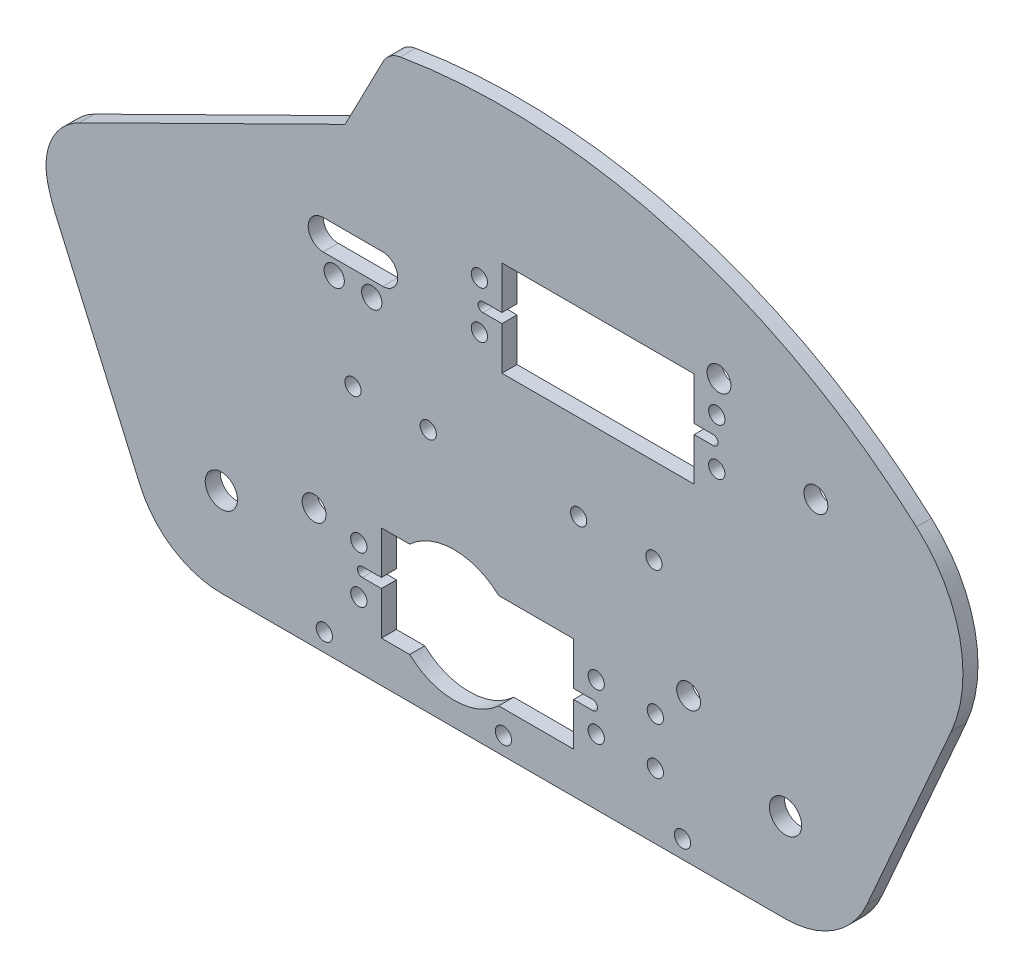
SolidWorks part; units mm, degrees
ref_plane "Front Plane" through (0, 0, 0) normal (0, 0, 1) x (1, 0, 0)
ref_plane "Top Plane" through (0, 0, 0) normal (0, 1, 0) x (1, 0, 0)
ref_plane "Right Plane" through (0, 0, 0) normal (1, 0, 0) x (0, 0, -1)
sketch "Sketch1" plane through (0, 0, 0) normal (0, 0, 1) x (1, 0, 0)
  line L8 (0, 18.9078) -> (120.015, 18.9078) construction
  line L18 (155.2575, 52.1157) -> (-35.2425, 52.1157) construction
  line L37 (0, 0) -> (120.015, 0)
  line L42 (19.7347, 25.5664) -> (0, 18.9078) construction
  line L54 (155.2575, 52.1157) -> (137.3256, 11.3022)
  line L55 (60.0075, 52.1157) -> (60.0075, 18.9078) construction
  line L56 (-35.2425, 52.1157) -> (-17.3106, 11.3022)
  line L58 (147.8628, 86.1549) -> (-27.8478, 86.1549) construction
  circle A21 centre (120.015, 18.9078) radius 3.429
  circle A22 centre (0, 18.9078) radius 3.429
  arc A25 (137.3256, 11.3022) -> (120.015, 0) centre (120.015, 18.9078) cw
  arc A26 (0, 0) -> (-17.3106, 11.3022) centre (0, 18.9078) cw
  circle A27 centre (19.7347, 25.5664) radius 2.54
  arc A28 (147.8628, 86.1549) -> (-27.8478, 86.1549) centre (60.0075, -12.2157) ccw
  arc A29 (147.8628, 86.1549) -> (155.2575, 52.1157) centre (128.1135, 64.0417) cw
  arc A30 (-27.8478, 86.1549) -> (-35.2425, 52.1157) centre (-8.0985, 64.0417) ccw
  dimension "D5" = 18.9078
  dimension "D8" = 29.6484
  dimension "D3" = 52.1157
  dimension "D2" = 6.858
  dimension "D10" = 5.08
  dimension "D1" = 190.5
  dimension "D4" = 18.645
  dimension "D6" = 20.8278
  dimension "D7" = 120.015
  dimension "D9" = 34.0392
extrude "Boss-Extrude1" add sketch "Sketch1" along normal blind 3.2004
sketch "Sketch2" plane through (0, 0, 0) normal (0, 0, -1) x (-1, 0, 0)
  line L1 (-155.2575, 52.1157) -> (35.2425, 52.1157) construction
  line L28 (-92.0115, 52.1157) -> (-76.0095, 52.1157) construction
  line L29 (-76.0095, 52.1157) -> (-44.0055, 52.1157) construction
  line L30 (-44.0055, 52.1157) -> (-28.0035, 52.1157) construction
  circle A0 centre (-92.0115, 52.1157) radius 1.7272
  circle A1 centre (-76.0095, 52.1157) radius 1.7272
  circle A2 centre (-44.0055, 52.1157) radius 1.7272
  circle A3 centre (-28.0035, 52.1157) radius 1.7272
  point P11 (-36.0045, 52.1157)
  point P16 (-84.0105, 52.1157)
  dimension "D3" = 3.4544
  dimension "D2" = 16.002
  dimension "D4" = 48.006
extrude "Cut-Extrude1" cut sketch "Sketch2" against normal blind 3.2004
sketch "Sketch5" plane through (0, 0, 0) normal (0, 0, -1) x (-1, 0, 0)
  line L0 (0, 18.9078) -> (-120.015, 18.9078) construction
  line L5 (-92.3222, 13.9078) -> (-92.3222, 23.9078) construction
  line L6 (-74.944, 29.0678) -> (-74.944, 8.7478)
  line L7 (-34.05, 29.0678) -> (-34.05, 8.7478)
  line L12 (-54.497, 29.0678) -> (-54.497, 8.7478) construction
  line L13 (-79.747, 13.9078) -> (-79.747, 23.9078) construction
  line L14 (-29.247, 13.9078) -> (-29.247, 23.9078) construction
  line L15 (-79.747, 18.9078) -> (-29.247, 18.9078) construction
  line L19 (-92.3222, 18.9078) -> (-79.747, 18.9078) construction
  line L21 (-74.944, 8.7478) -> (-34.05, 8.7478)
  line L25 (-74.944, 29.0678) -> (-34.05, 29.0678)
  circle A0 centre (-79.747, 23.9078) radius 1.7272
  circle A1 centre (-29.247, 13.9078) radius 1.7272
  circle A2 centre (-29.247, 23.9078) radius 1.7272
  circle A3 centre (-79.747, 13.9078) radius 1.7272
  circle A6 centre (0, 18.9078) radius 3.429 construction
  circle A9 centre (-92.3222, 23.9078) radius 1.7272
  circle A10 centre (-92.3222, 13.9078) radius 1.7272
  point P8 (-44.45, 18.9078)
  point P9 (-54.497, 18.9078)
  dimension "D2" = 3.4544
  dimension "D3" = 40.894
  dimension "D5" = 10.4
  dimension "D1" = 50.5
  dimension "D4" = 20.32
  dimension "D6" = 44.45
  dimension "D7" = 10
  dimension "D8" = 12.5752
extrude "Cut-Extrude3" cut sketch "Sketch5" against normal through all
sketch "Sketch6" plane through (0, 0, 3.2004) normal (0, 0, 1) x (1, 0, 0)
  line L3 (79.747, 18.9078) -> (29.247, 18.9078) construction
  line L4 (29.986, 19.9238) -> (34.05, 19.9238)
  line L5 (29.986, 19.9238) -> (29.986, 17.8918) construction
  line L7 (29.986, 17.8918) -> (34.05, 17.8918)
  line L8 (34.05, 19.9238) -> (34.05, 17.8918)
  line L9 (74.944, 19.9238) -> (79.008, 19.9238)
  line L10 (74.944, 19.9238) -> (74.944, 17.8918)
  line L11 (74.944, 17.8918) -> (79.008, 17.8918)
  line L12 (79.008, 19.9238) -> (79.008, 17.8918) construction
  line L13 (34.05, 8.7478) -> (34.05, 29.0678) construction
  line L14 (74.944, 29.0678) -> (74.944, 8.7478) construction
  arc A6 (79.008, 19.9238) -> (79.008, 17.8918) centre (79.008, 18.9078) cw
  arc A7 (29.986, 19.9238) -> (29.986, 17.8918) centre (29.986, 18.9078) ccw
  point P22 (34.05, 18.9078)
  point P23 (74.944, 18.9078)
  dimension "D4" = 4.064
  dimension "D5" = 2.032
extrude "Cut-Extrude4" cut sketch "Sketch6" against normal up to surface (3.2004 mm away) up to face at (90.595, 23.9078, 0)
sketch "Sketch8" plane through (0, 0, 3.2004) normal (0, 0, 1) x (1, 0, 0)
  line L0 (21.9075, 3.81) -> (98.1075, 3.81) construction
  line L1 (60.0075, 7.62) -> (60.0075, 0) construction
  line L2 (0, 0) -> (120.015, 0) construction
  circle A0 centre (21.9075, 3.81) radius 1.7272
  circle A1 centre (60.0075, 3.81) radius 1.7272
  circle A2 centre (98.1075, 3.81) radius 1.7272
  point P6 (60.0075, 3.81)
  dimension "D3" = 3.4544
  dimension "D1" = 76.2
  dimension "D2" = 7.62
extrude "Cut-Extrude6" cut sketch "Sketch8" against normal up to surface (3.2004 mm away) up to face at (54.497, 18.9078, 0)
sketch "Sketch9" plane through (0, 0, 0) normal (0, 0, -1) x (-1, 0, 0)
  line L5 (-29.247, 13.9078) -> (-29.247, 23.9078) construction
  line L7 (-80.1415, 90.6958) -> (-80.1415, 70.3758) construction
  line L12 (-59.6945, 90.6958) -> (-59.6945, 70.3758)
  line L13 (-54.497, 29.0678) -> (-54.497, 8.7478) construction
  line L14 (-74.944, 8.7478) -> (-34.05, 8.7478) construction
  line L18 (-100.5885, 70.3758) -> (-100.5885, 90.6958)
  line L19 (-105.3915, 75.5358) -> (-105.3915, 85.5358) construction
  line L20 (-54.8915, 75.5358) -> (-54.8915, 85.5358) construction
  line L24 (-105.3915, 80.5358) -> (-54.8915, 80.5358) construction
  line L30 (-100.5885, 70.3758) -> (-59.6945, 70.3758)
  line L31 (-100.5885, 90.6958) -> (-59.6945, 90.6958)
  line L32 (-105.8603, 92.4374) -> (-126.4745, 80.5358) construction
  line L34 (-126.4745, 80.5358) -> (-111.6995, 46.9073) construction
  line L35 (-111.6995, 46.9073) -> (-146.2916, 31.7089) construction
  line L37 (-137.3256, 11.3022) -> (-155.2575, 52.1157) construction
  line L38 (-34.05, 29.0678) -> (-34.05, 8.7478) construction
  circle A6 centre (-19.7347, 25.5664) radius 2.54 construction
  circle A7 centre (-105.3915, 85.5358) radius 1.7272
  circle A8 centre (-105.8603, 92.4374) radius 2.54
  circle A9 centre (-54.8915, 75.5358) radius 1.7272
  circle A10 centre (-54.8915, 85.5358) radius 1.7272
  circle A11 centre (-105.3915, 75.5358) radius 1.7272
  circle A13 centre (-126.4745, 80.5358) radius 2.54
  point P14 (-80.1415, 80.5358)
  point P21 (-89.9915, 80.5358)
  dimension "D2" = 30
  dimension "D3" = 37.7837
  dimension "D5" = 3.4544
  dimension "D6" = 15.4
  dimension "D4" = 36.7311
  dimension "D7" = 23.8032
  dimension "D8" = 50.5
extrude "Cut-Extrude8" cut sketch "Sketch9" against normal up to surface (3.2004 mm away) up to face at (23.6347, 3.81, 3.2004)
sketch "Sketch10" plane through (0, 0, 3.2004) normal (0, 0, 1) x (1, 0, 0)
  line L0 (-24.9698, 88.6515) -> (-19.2074, 77.0076)
  line L1 (-19.2074, 77.0076) -> (26.3335, 99.5452)
  line L2 (26.3335, 99.5452) -> (35.569, 117.3917)
  arc A2 (35.569, 117.3917) -> (-24.9698, 88.6515) centre (60.0075, -12.2157) ccw
  arc A4 (147.8628, 86.1549) -> (-27.8478, 86.1549) centre (60.0075, -12.2157) ccw construction
  dimension "D1" = 50.8126
  dimension "D2" = 20.0946
  dimension "D3" = 12.9917
  dimension "D4" = 143.691
  dimension "D5" = 3.81
extrude "Cut-Extrude9" cut sketch "Sketch10" against normal up to surface (3.2004 mm away) up to face at (103.6643, 75.5358, 0)
fillet "Fillet1" radius 5.08 2 edges at (35.569, 117.3917, 1.6002) (-24.9698, 88.6515, 1.6002)
sketch "Sketch11" plane through (0, 0, 0) normal (0, 0, -1) x (-1, 0, 0)
  line L1 (-34.3535, 80.0557) -> (-21.6535, 80.0557)
  line L2 (-34.3535, 80.0557) -> (-34.3535, 73.7057) construction
  line L3 (-34.3535, 73.7057) -> (-21.6535, 73.7057)
  line L4 (-21.6535, 80.0557) -> (-21.6535, 73.7057) construction
  line L7 (0, 0) -> (-120.015, 0) construction
  line L9 (-32.004, 70.5307) -> (-24.003, 70.5307) construction
  line L11 (-28.0035, 73.7057) -> (-28.0035, 70.5307) construction
  arc A0 (-21.6535, 80.0557) -> (-21.6535, 73.7057) centre (-21.6535, 76.8807) cw
  arc A1 (-34.3535, 80.0557) -> (-34.3535, 73.7057) centre (-34.3535, 76.8807) ccw
  circle A5 centre (-28.0035, 52.1157) radius 1.7272 construction
  circle A6 centre (-32.004, 70.5307) radius 2.159
  circle A7 centre (-24.003, 70.5307) radius 2.159
  dimension "D3" = 21.59
  dimension "D7" = 4.318
  dimension "D1" = 12.7
  dimension "D2" = 6.35
  dimension "D4" = 6.35
  dimension "D5" = 3.175
  dimension "D6" = 8.001
extrude "Cut-Extrude10" cut sketch "Sketch11" against normal up to surface (3.2004 mm away) up to face at (41.5205, 61.5939, 3.2004)
sketch "Sketch12" plane through (0, 0, 0) normal (0, 0, -1) x (-1, 0, 0)
  line L0 (-100.5885, 90.6958) -> (-100.5885, 70.3758) construction
  line L1 (-59.6945, 70.3758) -> (-59.6945, 90.6958) construction
  line L4 (-104.6525, 81.5518) -> (-100.5885, 81.5518)
  line L5 (-104.6525, 81.5518) -> (-104.6525, 79.5198) construction
  line L7 (-104.6525, 79.5198) -> (-100.5885, 79.5198)
  line L8 (-100.5885, 81.5518) -> (-100.5885, 79.5198)
  line L9 (-59.6945, 81.5518) -> (-55.6305, 81.5518)
  line L10 (-59.6945, 81.5518) -> (-59.6945, 79.5198)
  line L11 (-59.6945, 79.5198) -> (-55.6305, 79.5198)
  line L12 (-55.6305, 81.5518) -> (-55.6305, 79.5198) construction
  arc A6 (-55.6305, 81.5518) -> (-55.6305, 79.5198) centre (-55.6305, 80.5358) cw
  arc A7 (-104.6525, 81.5518) -> (-104.6525, 79.5198) centre (-104.6525, 80.5358) ccw
  point P22 (-100.5885, 80.5358)
  point P23 (-59.6945, 80.5358)
  dimension "D4" = 4.064
  dimension "D5" = 2.032
extrude "Cut-Extrude11" cut sketch "Sketch12" against normal up to surface (3.2004 mm away) up to face at (28.0035, 76.8807, 3.2004)
sketch "Sketch13" plane through (0, 0, 0) normal (0, 0, -1) x (-1, 0, 0)
  line L4 (-79.747, 18.9078) -> (-29.247, 18.9078) construction
  circle A0 centre (-49.53, 18.9078) radius 13.8852
  dimension "D1" = 27.7704
  dimension "D2" = 5.08
extrude "Cut-Extrude12" cut sketch "Sketch13" against normal up to surface (3.2004 mm away) up to face at (28.0035, 76.8807, 3.2004)
sketch "Sketch14" plane through (0, 0, 0) normal (0, 0, -1) x (-1, 0, 0)
  line L0 (-99.4008, 30.8094) -> (-120.015, 18.9078) construction
  line L2 (0, 0) -> (-120.015, 0) construction
  circle A2 centre (-99.4008, 30.8094) radius 2.54
  circle A4 centre (-120.015, 18.9078) radius 3.429 construction
  circle A5 centre (-19.7347, 25.5664) radius 2.54 construction
  dimension "D1" = 30
  dimension "D2" = 23.8032
extrude "Cut-Extrude13" cut sketch "Sketch14" against normal up to surface (3.2004 mm away) up to face at (28.0035, 76.8807, 3.2004)
sketch "Sketch15" plane through (0, 0, 0) normal (0, 0, -1) x (-1, 0, 0)
  line L0 (19.2074, 77.0076) -> (-26.3335, 99.5452) construction
  line L1 (33.7711, 106.436) -> (93.3026, 68.041)
  line L2 (33.7711, 106.436) -> (19.2074, 77.0076)
  line L3 (19.2074, 77.0076) -> (77.9126, 47.9552)
  line L4 (93.3026, 68.041) -> (77.9126, 47.9552)
  line L5 (21.9565, 82.5627) -> (19.2074, 77.0076) construction
extrude "Cut-Extrude14" cut sketch "Sketch15" against normal up to surface (3.2004 mm away) up to face at (96.8608, 30.8094, 3.2004)
fillet "Fillet2" radius 12.7 1 edges at (-37.4866, 67.9615, 1.6002)
